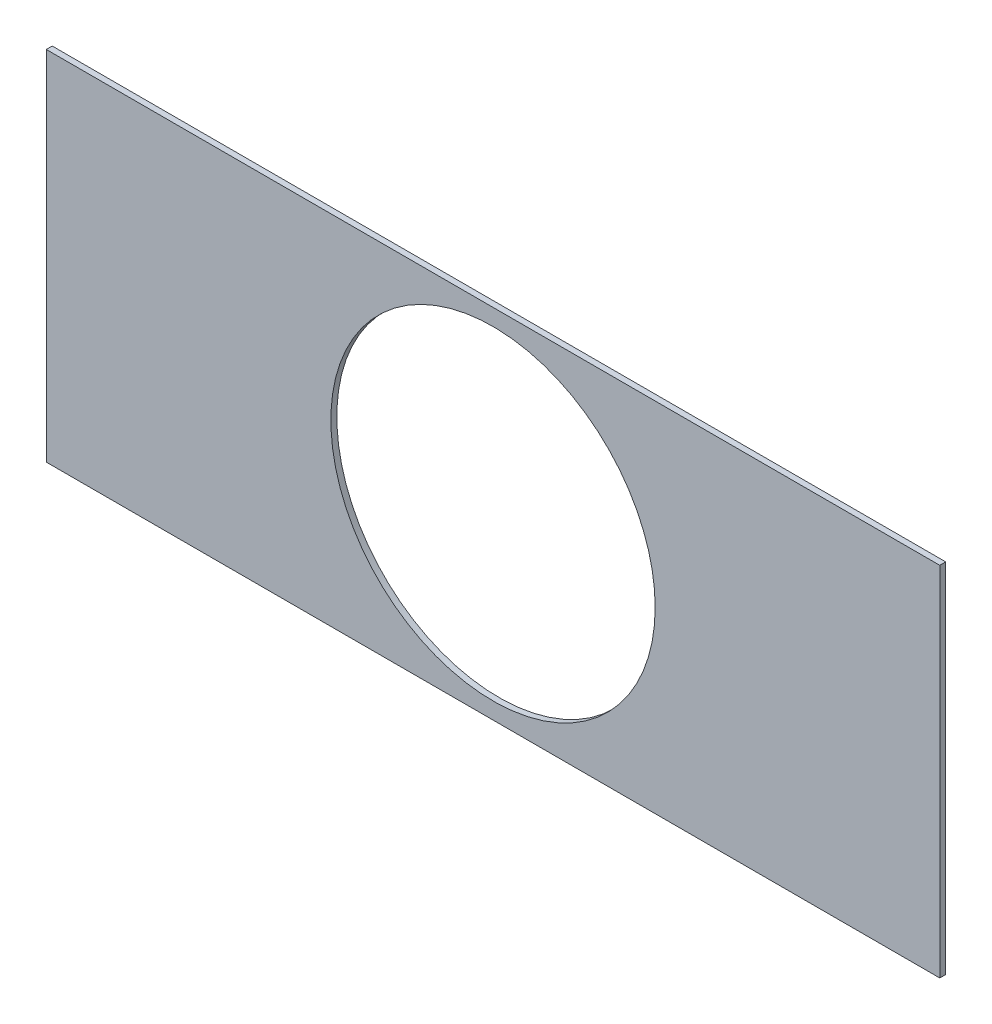
SolidWorks part; units mm, degrees
material "Acrylic (Medium-high impact)"
ref_plane "Front Plane" through (0, 0, 0) normal (0, 0, 1) x (1, 0, 0)
ref_plane "Top Plane" through (0, 0, 0) normal (0, 1, 0) x (1, 0, 0)
ref_plane "Right Plane" through (0, 0, 0) normal (1, 0, 0) x (0, 0, -1)
sketch "Sketch1" plane through (0, 0, 0) normal (0, 0, 1) x (1, 0, 0)
  line L1 (150, -36.7008) -> (-150, -36.7008)
  line L2 (150, -36.7008) -> (150, 83.2992)
  line L3 (150, 83.2992) -> (-150, 83.2992)
  line L4 (-150, -36.7008) -> (-150, 83.2992)
  line L5 (150, -36.7008) -> (-150, 83.2992) construction
  line L6 (150, 83.2992) -> (-150, -36.7008) construction
  circle A0 centre (0, 23.2992) radius 54.4501
  point P0 (0, 23.2992)
  dimension "D1" = 300
  dimension "D2" = 120
extrude "Boss-Extrude1" add sketch "Sketch1" along normal blind 2
